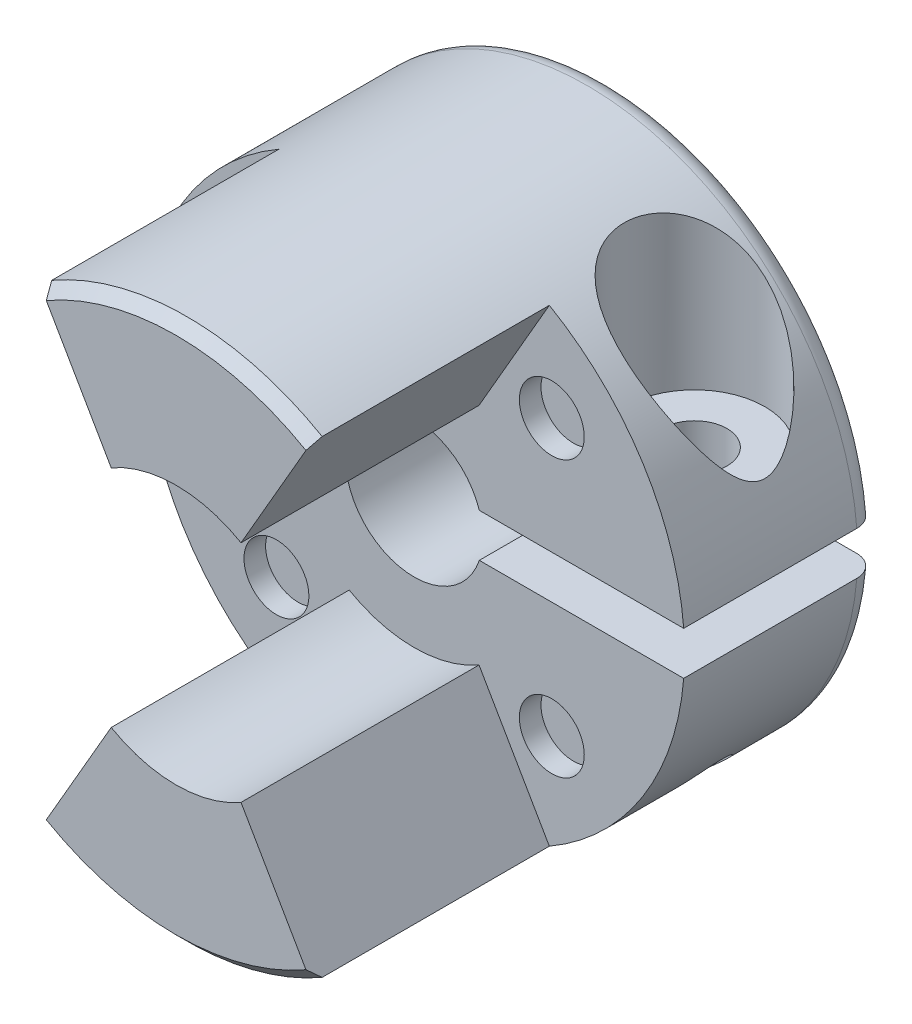
SolidWorks part; units mm, degrees
material "Liga 6061"
ref_plane "Plano frontal" through (0, 0, 0) normal (0, 0, 1) x (1, 0, 0)
ref_plane "Plano superior" through (0, 0, 0) normal (0, 1, 0) x (1, 0, 0)
ref_plane "Plano direito" through (0, 0, 0) normal (1, 0, 0) x (0, 0, -1)
sketch "Esboço1" plane through (0, 0, 0) normal (0, 0, 1) x (1, 0, 0)
  circle A0 centre (0, 0) radius 12.5
  dimension "D1" = 25
extrude "Ressalto-extrusão1" add sketch "Esboço1" along normal blind 20
sketch "Esboço2" plane through (0, 0, 20) normal (0, 0, 1) x (1, 0, 0)
  line L0 (0, 0) -> (0, 12.5) construction
  line L1 (0, 0) -> (6.25, 10.8253)
  line L2 (6.25, -10.8253) -> (0, 0)
  circle A0 centre (0, 0) radius 12.5 construction
  arc A2 (6.25, 10.8253) -> (6.25, -10.8253) centre (0, 0) cw
  dimension "D1" = 120
  dimension "D2" = 30
extrude "Corte-extrusão3" cut sketch "Esboço2" against normal blind 11
sketch "Esboço3" plane through (0, 0, 0) normal (0, 0, -1) x (-1, 0, 0)
  circle A0 centre (0, 0) radius 3.175
  dimension "D1" = 6.35
extrude "Corte-extrusão4" cut sketch "Esboço3" against normal through all
mirror "Espelhar1" about plane through (0, 0, 0) normal (1, 0, 0) of "Corte-extrusão3"
sketch "Esboço6" plane through (0, 0, 9) normal (0, 0, 1) x (1, 0, 0)
  line L1 (1, 1) -> (13, 1)
  line L2 (1, 1) -> (1, -1)
  line L3 (1, -1) -> (13, -1)
  line L4 (13, 1) -> (13, -1)
  line L5 (1, 1) -> (13, -1) construction
  line L6 (1, -1) -> (13, 1) construction
  point P0 (7, 0)
  dimension "D1" = 2
  dimension "D2" = 12
  dimension "D3" = 7
extrude "Corte-extrusão5" cut sketch "Esboço6" against normal through all
sketch "Esboço7" plane through (0, 1, 0) normal (0, -1, 0) x (1, 0, 0)
  line L0 (12.4599, 9) -> (12.4599, 0) construction
  circle A0 centre (8.4599, 4.5) radius 3.25
  point P4 (12.4599, 4.5)
  dimension "D1" = 6.5
  dimension "D2" = 4
extrude "Corte-extrusão6" cut sketch "Esboço7" against normal through all from offset 3 offset against normal yes
hole_wizard "Furo roscado de M3x0.51" positions "Esboço9" profile "Esboço8" tap size "M3x0.5" standard "Ansi Metric" end condition through all
sketch "Esboço9" plane through (0, 4, 0) normal (0, 1, 0) x (1, 0, 0)
  point P0 (8.4599, -4.5)
sketch "Esboço8" plane through (8.4599, 4, 4.5) normal (1, 0, 0) x (0, 0, 1)
  line L0 (0, 0) -> (0, 16.5)
  line L1 (0, 16.5) -> (1.25, 16.5)
  line L2 (1.25, 16.5) -> (1.25, 0)
  line L5 (1.25, 0) -> (0, 0)
  line L11 (0, -6.35) -> (0, 107.95) construction
  dimension "Thru Tap Drill Dia." = 2.5
  dimension "Thru Tap Drill Depth" = 16.5
cosmetic thread "Rosca de furo2" parameters "D2"=3
fillet "Filete1" radius 1 1 edges at (-12.5, 0, 0)
sketch "Esboço10" plane through (0, 0, 9) normal (0, 0, 1) x (1, 0, 0)
  line L0 (0, 0) -> (0, -3.9553) construction
  line L1 (6.364, -6.364) -> (0, 0) construction
  circle A0 centre (6.364, -6.364) radius 1.5
  dimension "D1" = 3
  dimension "D2" = 9
  dimension "D3" = 45
extrude "Corte-extrusão7" cut sketch "Esboço10" against normal blind 1
chamfer "Chanfro1" distance 0.5 angle 45 2 edges at (0, 12.5, 20) (0, -12.5, 20)
sketch "Esboço11" plane through (0, 4, 0) normal (0, 1, 0) x (1, 0, 0)
  circle A0 centre (8.4599, -4.5) radius 1.5
  dimension "D1" = 3
extrude "Corte-extrusão8" cut sketch "Esboço11" against normal up to next
sketch "Esboço12" plane through (0, 0, 20) normal (0, 0, 1) x (1, 0, 0)
  circle A0 centre (0, 0) radius 6
  dimension "D1" = 12
extrude "Corte-extrusão9" cut sketch "Esboço12" against normal up to surface (11 mm away) up to face at (6.1708, 4.1179, 9)
pattern_circular "PadrãoCircular1" count 4 over 360 about axis through (0, 0, 0) along (0, 0, 1) of "Corte-extrusão7"
chamfer "Chanfro2" distance 0.5 angle 45 1 edges at (-3.175, 0, 0)
